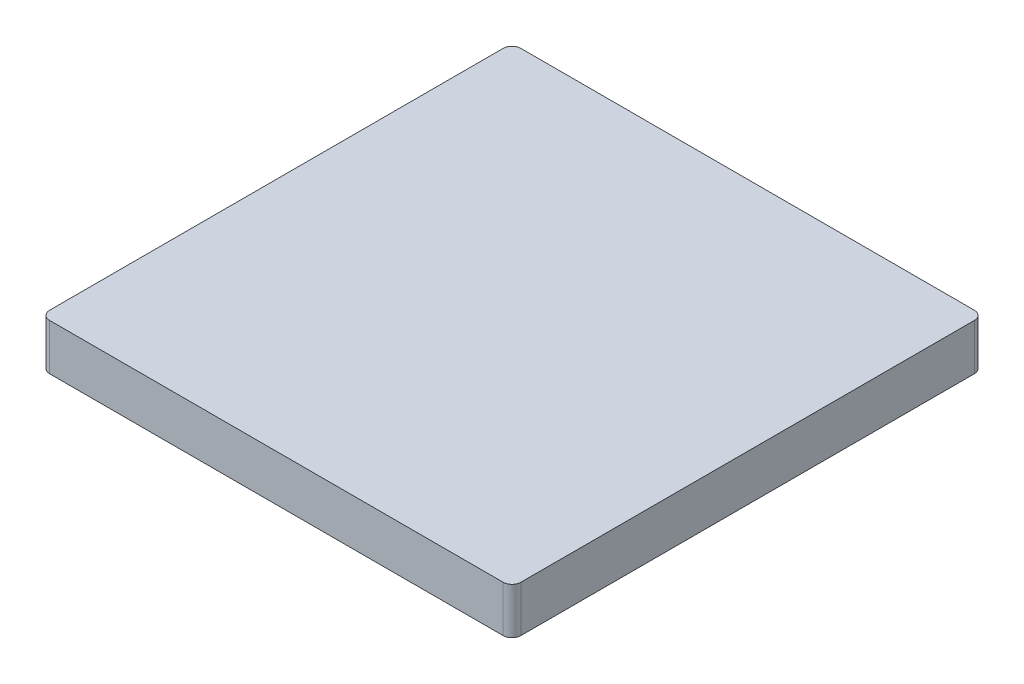
SolidWorks part; units mm, degrees
ref_plane "Front Plane" through (0, 0, 0) normal (0, 0, 1) x (1, 0, 0)
ref_plane "Top Plane" through (0, 0, 0) normal (0, 1, 0) x (1, 0, 0)
ref_plane "Right Plane" through (0, 0, 0) normal (1, 0, 0) x (0, 0, -1)
sketch "Sketch1" plane through (0, 0, 0) normal (0, 1, 0) x (1, 0, 0)
  line L1 (-8, -8) -> (8, -8)
  line L2 (-8, -8) -> (-8, 8)
  line L3 (-8, 8) -> (8, 8)
  line L4 (8, -8) -> (8, 8)
  line L5 (-8, -8) -> (8, 8) construction
  line L6 (-8, 8) -> (8, -8) construction
  point P0 (0, 0)
  dimension "D1" = 16
extrude "Boss-Extrude1" add sketch "Sketch1" along normal blind 1.57
fillet "Fillet1" radius 0.3 4 edges at (-8, 0.785, -8) (8, 0.785, -8) (8, 0.785, 8) (-8, 0.785, 8)
